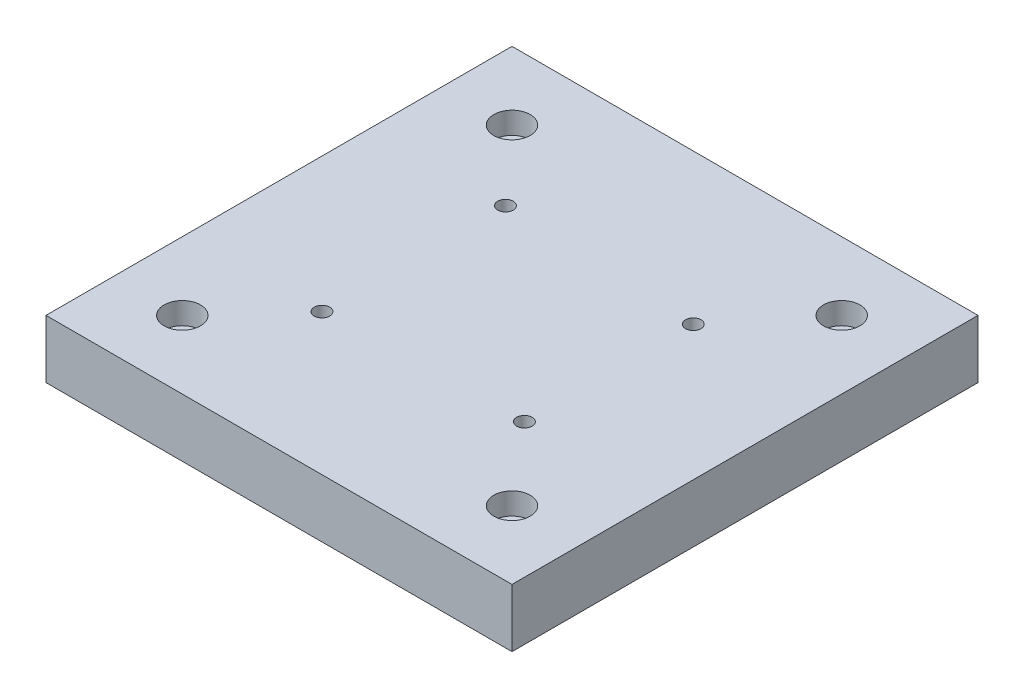
SolidWorks part; units mm, degrees
material "6061-T4 (SS)"
ref_plane "Front Plane" through (0, 0, 0) normal (0, 0, 1) x (1, 0, 0)
ref_plane "Top Plane" through (0, 0, 0) normal (0, 1, 0) x (1, 0, 0)
ref_plane "Right Plane" through (0, 0, 0) normal (1, 0, 0) x (0, 0, -1)
sketch "Sketch1" plane through (0, 0, 0) normal (0, 1, 0) x (1, 0, 0)
  line L0 (101.6, 0) -> (101.6, 203.2) construction
  line L1 (0, 0) -> (203.2, 0)
  line L2 (0, 0) -> (0, 203.2)
  line L3 (0, 203.2) -> (203.2, 203.2)
  line L4 (203.2, 0) -> (203.2, 203.2)
  point P7 (101.6, 101.6)
  dimension "D1" = 203.2
  dimension "D2" = 203.2
extrude "Boss-Extrude1" add sketch "Sketch1" along normal blind 25.4
sketch "Sketch3" plane through (0, 25.4, 0) normal (0, 1, 0) x (1, 0, 0)
  line L0 (101.6, 203.2) -> (101.6, 0) construction
  line L1 (203.2, 203.2) -> (0, 203.2) construction
  line L2 (0, 0) -> (203.2, 0) construction
  line L3 (101.6, 101.6) -> (203.2, 101.6) construction
  line L4 (203.2, 0) -> (203.2, 203.2) construction
ref_plane "Plane1" through (101.6, 0, 0) normal (1, 0, 0) x (0, 0, -1)
sketch "Sketch4" plane through (101.6, 0, 0) normal (1, 0, 0) x (0, 0, -1)
  line L0 (101.6, 25.4) -> (101.6, 141.7055) construction
sketch "Sketch5" plane through (0, 25.4, 0) normal (0, 1, 0) x (1, 0, 0)
  circle A0 centre (144.4625, 64.135) radius 1.6
  circle A1 centre (144.4625, 137.795) radius 1.6
  circle A2 centre (58.7375, 141.605) radius 1.6
  circle A3 centre (58.7375, 61.595) radius 1.6
  circle A4 centre (58.7375, 61.595) radius 1.6 construction
  circle A5 centre (144.4625, 64.135) radius 1.6 construction
  circle A6 centre (144.4625, 137.795) radius 1.6 construction
  circle A7 centre (58.7375, 141.605) radius 1.6 construction
hole_wizard "CBORE for 1/4 Socket Head Cap Screw1" positions "Sketch8" profile "Sketch7" counterbore size "1/4" standard "ANSI Inch" end condition through all
sketch "Sketch8" plane through (0, 0, 0) normal (0, -1, 0) x (-1, 0, 0)
  point P0 (-144.4625, 64.135)
  point P2 (-58.7375, 61.595)
  point P4 (-58.7375, 141.605)
  point P6 (-144.4625, 137.795)
sketch "Sketch7" plane through (144.4625, 0, -64.135) normal (1, 0, 0) x (0, 0, -1)
  line L0 (0, 0) -> (0, 25.4)
  line L1 (0, 25.4) -> (3.3782, 25.4)
  line L3 (3.3782, 25.4) -> (3.3782, 18.35)
  line L4 (3.3782, 18.35) -> (5.5562, 18.35)
  line L5 (5.5562, 18.35) -> (5.5562, 0)
  line L7 (5.5562, 0) -> (0, 0)
  line L11 (0, -6.35) -> (0, 107.95) construction
  dimension "Thru Hole Dia." = 6.7564
  dimension "Thru Hole Depth" = 25.4
  dimension "C'Bore Dia." = 11.1125
  dimension "C'Bore Depth" = 18.35
sketch "Sketch9" plane through (0, 25.4, 0) normal (0, 1, 0) x (1, 0, 0)
  line L0 (101.6, 0) -> (101.6, 203.2) construction
  line L1 (0, 0) -> (203.2, 0) construction
  line L2 (203.2, 203.2) -> (0, 203.2) construction
  line L3 (101.6, 101.6) -> (203.2, 101.6) construction
  line L4 (203.2, 0) -> (203.2, 203.2) construction
  line L5 (101.6, 101.6) -> (0, 101.6) construction
  line L6 (0, 203.2) -> (0, 0) construction
  line L7 (173.482, 173.482) -> (173.482, 29.718) construction
  line L8 (29.718, 173.482) -> (29.718, 29.718) construction
  point P10 (173.482, 173.482)
  point P14 (101.6, 50.8)
  point P15 (101.6, 152.4)
  point P18 (29.718, 173.482)
  point P19 (152.4, 101.6)
  point P20 (173.482, 29.718)
  point P23 (173.482, 101.6)
  point P24 (50.8, 101.6)
  point P27 (29.718, 29.718)
  dimension "D1" = 71.882
  dimension "D2" = 71.882
  dimension "D3" = 50.8
  dimension "D4" = 50.8
hole_wizard "CBORE for 3/8 Socket Head Cap Screw1" positions "Sketch10" profile "Sketch12" counterbore size "3/8" standard "ANSI Inch" end condition through all
sketch "Sketch10" plane through (0, 25.4, 0) normal (0, 1, 0) x (1, 0, 0)
  point P0 (29.718, 173.482)
  point P6 (29.718, 29.718)
  point P12 (173.482, 29.718)
  point P18 (173.482, 173.482)
sketch "Sketch12" plane through (29.718, 25.4, -173.482) normal (1, 0, 0) x (0, 0, 1)
  line L0 (0, 0) -> (0, 25.4)
  line L1 (0, 25.4) -> (5.0419, 25.4)
  line L3 (5.0419, 25.4) -> (5.0419, 9.525)
  line L4 (5.0419, 9.525) -> (7.9375, 9.525)
  line L5 (7.9375, 9.525) -> (7.9375, 0)
  line L7 (7.9375, 0) -> (0, 0)
  line L11 (0, -6.35) -> (0, 107.95) construction
  dimension "Thru Hole Dia." = 10.0838
  dimension "Thru Hole Depth" = 25.4
  dimension "C'Bore Dia." = 15.875
  dimension "C'Bore Depth" = 9.525
hole_wizard "#4-40 Tapped Hole1" [suppressed] positions "Sketch13" profile "Sketch14" tap size "#4-40" standard "ANSI Inch"
sketch "Sketch13" plane through (0, 25.4, 0) normal (0, 1, 0) x (1, 0, 0)
  point P0 (58.7375, 61.595)
  point P2 (144.4625, 64.135)
  point P4 (144.4625, 137.795)
  point P6 (58.7375, 141.605)
sketch "Sketch14" plane through (58.7375, 25.4, -61.595) normal (1, 0, 0) x (0, 0, 1)
  line L0 (0, 0) -> (0, 25.4)
  line L1 (0, 25.4) -> (1.1303, 25.4)
  line L2 (1.1303, 25.4) -> (1.1303, 0)
  line L5 (1.1303, 0) -> (0, 0)
  line L11 (0, -6.35) -> (0, 107.95) construction
  dimension "Thru Tap Drill Dia." = 2.2606
  dimension "Thru Tap Drill Depth" = 25.4
cosmetic thread "Hole Thread1" [suppressed] parameters "D2"=2.8448
cosmetic thread "Hole Thread2" [suppressed] parameters "D2"=2.8448
cosmetic thread "Hole Thread3" [suppressed] parameters "D2"=2.8448
cosmetic thread "Hole Thread4" [suppressed] parameters "D2"=2.8448
